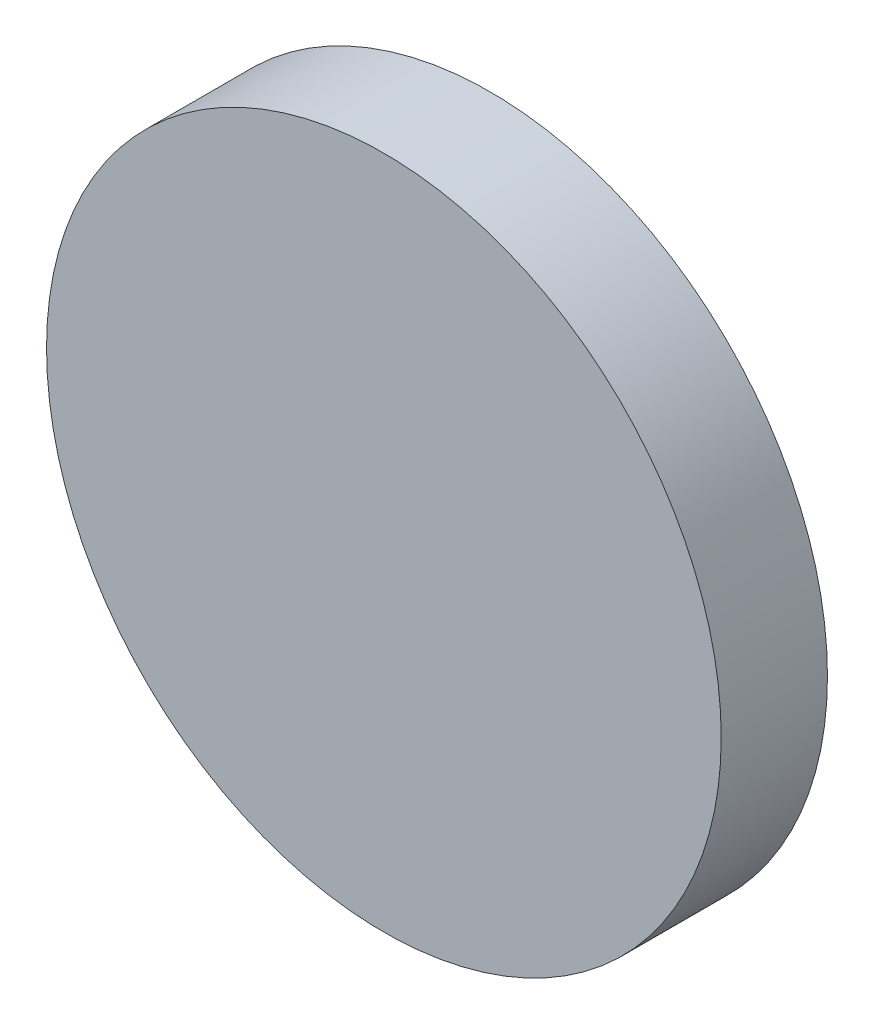
SolidWorks part; units mm, degrees
ref_plane "前视基准面" through (0, 0, 0) normal (0, 0, 1) x (1, 0, 0)
ref_plane "上视基准面" through (0, 0, 0) normal (0, 1, 0) x (1, 0, 0)
ref_plane "右视基准面" through (0, 0, 0) normal (1, 0, 0) x (0, 0, -1)
sketch "草图1" plane through (0, 0, 0) normal (0, 0, 1) x (1, 0, 0)
  circle A0 centre (0, 0) radius 12.7
  dimension "D1" = 25.4
extrude "凸台-拉伸1" add sketch "草图1" along normal blind 4 contours A0
